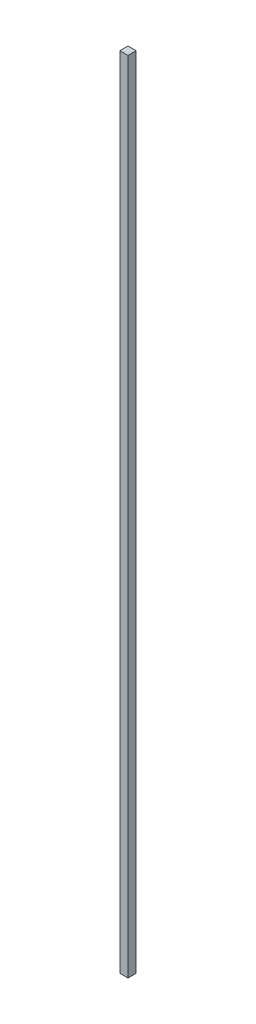
SolidWorks part; units mm, degrees
ref_plane "Front Plane" through (0, 0, 0) normal (0, 0, 1) x (1, 0, 0)
ref_plane "Top Plane" through (0, 0, 0) normal (0, 1, 0) x (1, 0, 0)
ref_plane "Right Plane" through (0, 0, 0) normal (1, 0, 0) x (0, 0, -1)
sketch "Sketch1" plane through (0, 0, 0) normal (0, 1, 0) x (1, 0, 0)
  line L1 (0, 0) -> (20, 0)
  line L2 (0, 0) -> (0, -20)
  line L3 (0, -20) -> (20, -20)
  line L4 (20, 0) -> (20, -20)
extrude "Boss-Extrude1" add sketch "Sketch1" along normal blind 1960
